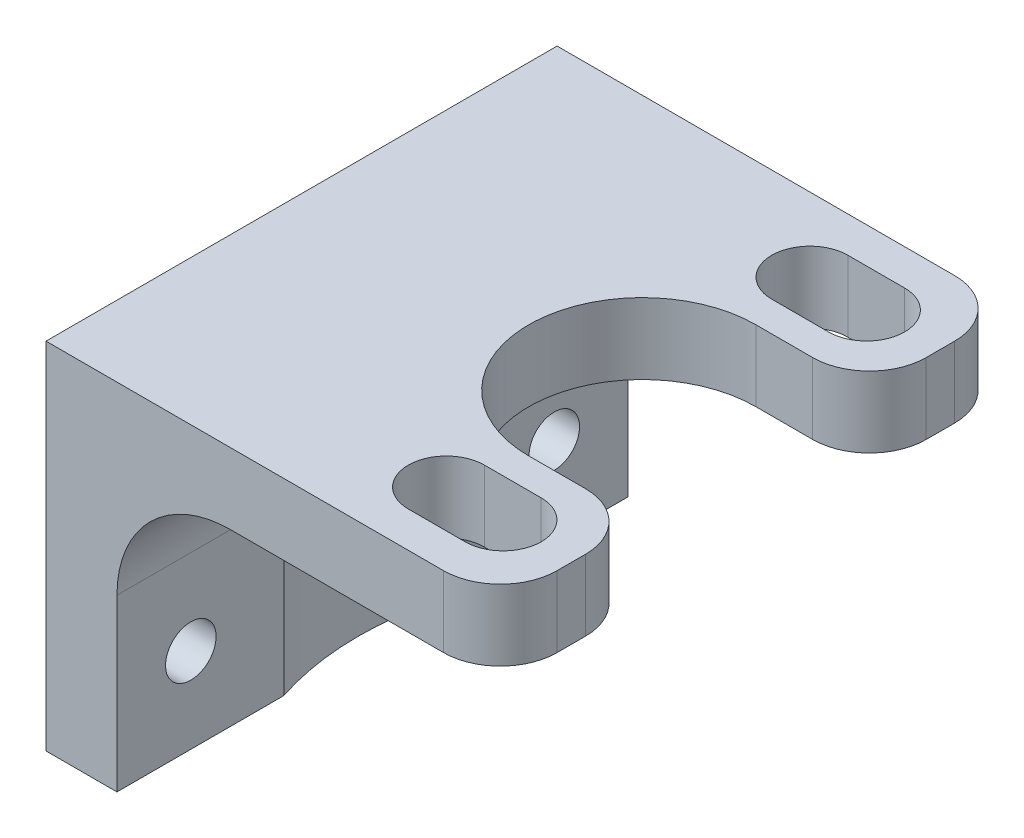
SolidWorks part; units mm, degrees
ref_plane "Front Plane" through (0, 0, 0) normal (0, 0, 1) x (1, 0, 0)
ref_plane "Top Plane" through (0, 0, 0) normal (0, 1, 0) x (1, 0, 0)
ref_plane "Right Plane" through (0, 0, 0) normal (1, 0, 0) x (0, 0, -1)
sketch "Sketch1" plane through (0, 0, 0) normal (0, 1, 0) x (1, 0, 0)
  line L1 (-10.16, -11.43) -> (10.16, -11.43)
  line L2 (-10.16, -11.43) -> (-10.16, 11.43)
  line L3 (-10.16, 11.43) -> (10.16, 11.43)
  line L4 (10.16, -11.43) -> (10.16, 11.43)
  line L5 (-10.16, -11.43) -> (10.16, 11.43) construction
  line L6 (-10.16, 11.43) -> (10.16, -11.43) construction
  point P0 (0, 0)
  dimension "D1" = 20.32
  dimension "D2" = 22.86
extrude "Boss-Extrude1" add sketch "Sketch1" along normal blind 3.175
fillet "Fillet1" radius 2.54 1 edges at (10.16, 1.5875, -11.43)
fillet "Fillet2" radius 2.54 1 edges at (10.16, 1.5875, 11.43)
sketch "Sketch2" plane through (0, 0, 0) normal (0, -1, 0) x (1, 0, 0)
  line L0 (-10.16, -11.43) -> (-10.16, 11.43) construction
  line L1 (7.62, -11.43) -> (-10.16, -11.43) construction
  line L2 (5.08, -5.08) -> (10.16, -5.08)
  line L3 (10.16, 8.89) -> (10.16, -8.89) construction
  line L4 (5.08, 5.08) -> (10.16, 5.08)
  line L5 (10.16, 5.08) -> (10.16, -5.08)
  arc A0 (5.08, 5.08) -> (5.08, -5.08) centre (5.08, 0) ccw
  dimension "D1" = 10.16
  dimension "D2" = 15.24
  dimension "D3" = 11.43
  dimension "D4" = 5.08
extrude "Cut-Extrude2" cut sketch "Sketch2" against normal through all
fillet "Fillet3" radius 2.54 1 edges at (10.16, 1.5875, 5.08)
fillet "Fillet4" radius 2.54 1 edges at (10.16, 1.5875, -5.08)
sketch "Sketch4" plane through (0, 0, 0) normal (0, -1, 0) x (1, 0, 0)
  line L0 (7.62, -11.43) -> (-10.16, -11.43) construction
  line L1 (-10.16, 11.43) -> (-6.985, 11.43)
  line L2 (-10.16, 11.43) -> (-10.16, -11.43)
  line L3 (-10.16, -11.43) -> (-6.985, -11.43)
  line L4 (-6.985, 11.43) -> (-6.985, -11.43)
  dimension "D1" = 3.175
extrude "Boss-Extrude2" add sketch "Sketch4" along normal blind 12.7
fillet "Fillet6" radius 5.08 2 edges
sketch "Sketch3" plane through (0, 0, 0) normal (0, -1, 0) x (1, 0, 0)
  line L0 (7.62, -11.43) -> (-1.905, -11.43) construction
  line L1 (-1.905, 11.43) -> (7.62, 11.43) construction
  line L2 (-10.16, -11.43) -> (-10.16, 11.43) construction
  circle A0 centre (5.08, 8.128) radius 0.9525
  circle A1 centre (5.08, -8.128) radius 0.9525
  dimension "D1" = 16.256
  dimension "D4" = 1.905
  dimension "D5" = 1.905
  dimension "D2" = 3.302
  dimension "D3" = 3.302
  dimension "D6" = 15.24
sketch "Sketch5" plane through (0, 0, 0) normal (0, -1, 0) x (1, 0, 0)
  line L0 (-10.16, 11.43) -> (-10.16, -11.43) construction
  line L1 (7.62, -11.43) -> (-1.905, -11.43) construction
  circle A0 centre (5.08, 0) radius 12.7
  dimension "D1" = 25.4
  dimension "D2" = 15.24
  dimension "D3" = 11.43
extrude "Cut-Extrude4" cut sketch "Sketch5" along normal through all
sketch "Sketch6" plane through (-6.985, 0, 0) normal (1, 0, 0) x (0, 0, -1)
  line L0 (11.43, -12.7) -> (11.43, -5.08) construction
  line L1 (-11.43, -12.7) -> (-11.43, -5.08) construction
  line L2 (11.43, -12.7) -> (3.9656, -12.7) construction
  circle A0 centre (-8.128, -8.89) radius 1.651
  circle A1 centre (8.128, -8.89) radius 1.651
  point P6 (-11.43, -8.89)
  dimension "D1" = 3.302
  dimension "D2" = 3.302
  dimension "D3" = 16.256
  dimension "D4" = 3.302
  dimension "D5" = 3.302
  dimension ".2" = 3.81
hole_wizard "#4-40 Tapped Hole3" positions "Sketch10" profile "Sketch9" tap size "#4-40" standard "ANSI Inch" end condition through all
sketch "Sketch10" plane through (-6.985, 0, 0) normal (1, 0, 0) x (0, 0, -1)
  point P0 (-8.128, -8.89)
  point P3 (8.128, -8.89)
sketch "Sketch9" plane through (-6.985, -8.89, 8.128) normal (0, 1, 0) x (0, 0, -1)
  line L0 (0, 0) -> (0, 3.175)
  line L1 (0, 3.175) -> (1.1303, 3.175)
  line L2 (1.1303, 3.175) -> (1.1303, 0)
  line L5 (1.1303, 0) -> (0, 0)
  line L11 (0, -6.35) -> (0, 107.95) construction
  dimension "Thru Tap Drill Dia." = 2.2606
  dimension "Thru Tap Drill Depth" = 3.175
cosmetic thread "Hole Thread1" parameters "D2"=2.8448
cosmetic thread "Hole Thread2" parameters "D2"=2.8448
sketch "Sketch11" plane through (0, 3.175, 0) normal (0, 1, 0) x (1, 0, 0)
  line L0 (0, 0) -> (12.0578, 0) construction
  line L1 (-10.16, 11.43) -> (-10.16, -11.43) construction
  line L2 (6.985, 9.8298) -> (4.445, 9.8298)
  line L3 (4.445, -6.4262) -> (6.985, -6.4262)
  line L4 (4.445, 6.4262) -> (6.985, 6.4262)
  line L5 (6.985, -9.8298) -> (4.445, -9.8298)
  arc A0 (6.985, 6.4262) -> (6.985, 9.8298) centre (6.985, 8.128) ccw
  arc A1 (4.445, -9.8298) -> (4.445, -6.4262) centre (4.445, -8.128) cw
  arc A2 (4.445, 9.8298) -> (4.445, 6.4262) centre (4.445, 8.128) ccw
  arc A3 (6.985, -6.4262) -> (6.985, -9.8298) centre (6.985, -8.128) cw
  dimension "D3" = 3.4036
  dimension "D4" = 2.54
  dimension "D1" = 16.256
  dimension "D2" = 17.145
extrude "Cut-Extrude6" cut sketch "Sketch11" against normal through all
